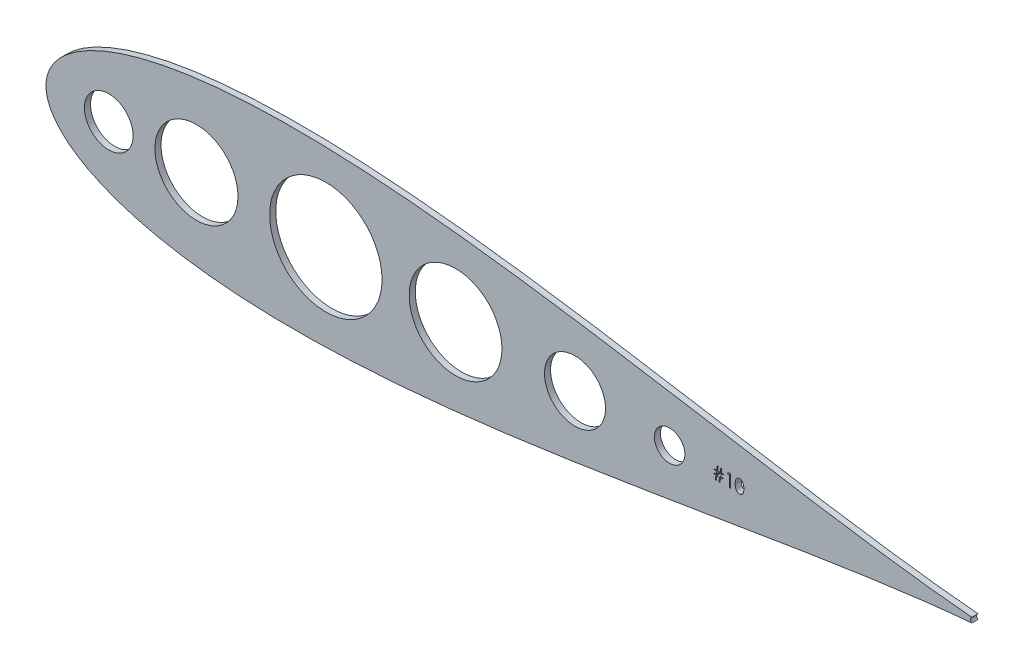
SolidWorks part; units mm, degrees
ref_plane "Front Plane" through (0, 0, 0) normal (0, 0, 1) x (1, 0, 0)
ref_plane "Top Plane" through (0, 0, 0) normal (0, 1, 0) x (1, 0, 0)
ref_plane "Right Plane" through (0, 0, 0) normal (1, 0, 0) x (0, 0, -1)
sketch "Model" plane through (0, 0, 0) normal (0, 0, 1) x (1, 0, 0)
  line L0 (632.1834, 567.3179) -> (632.1834, 572.0669)
  line L1 (632.6583, 567.3179) -> (632.1834, 567.3179)
  line L2 (632.6583, 572.6096) -> (632.6583, 567.3179)
  line L3 (631.6799, 572.6096) -> (632.6583, 572.6096)
  line L4 (631.3693, 572.0669) -> (631.6799, 572.6096)
  line L5 (632.1834, 572.0669) -> (631.3693, 572.0669)
  line L6 (629.6733, 570.71) -> (628.7595, 570.71)
  line L7 (629.6733, 571.0492) -> (629.6733, 570.71)
  line L8 (628.8104, 571.0492) -> (629.6733, 571.0492)
  line L9 (629.0648, 572.7453) -> (628.8104, 571.0492)
  line L10 (628.6556, 572.7453) -> (629.0648, 572.7453)
  line L11 (628.4012, 571.0492) -> (628.6556, 572.7453)
  line L12 (627.3179, 571.0492) -> (628.4012, 571.0492)
  line L13 (627.5723, 572.7453) -> (627.3179, 571.0492)
  line L14 (627.1631, 572.7453) -> (627.5723, 572.7453)
  line L15 (626.9087, 571.0492) -> (627.1631, 572.7453)
  line L16 (625.8741, 571.0492) -> (626.9087, 571.0492)
  line L17 (625.8741, 570.71) -> (625.8741, 571.0492)
  line L18 (626.8578, 570.71) -> (625.8741, 570.71)
  line L19 (626.6744, 569.4889) -> (626.8578, 570.71)
  line L20 (625.7384, 569.4889) -> (626.6744, 569.4889)
  line L21 (625.7384, 569.1497) -> (625.7384, 569.4889)
  line L22 (626.6236, 569.1497) -> (625.7384, 569.1497)
  line L23 (626.349, 567.3179) -> (626.6236, 569.1497)
  line L24 (626.7592, 567.3179) -> (626.349, 567.3179)
  line L25 (627.0338, 569.1497) -> (626.7592, 567.3179)
  line L26 (628.1161, 569.1497) -> (627.0338, 569.1497)
  line L27 (627.8415, 567.3179) -> (628.1161, 569.1497)
  line L28 (628.2518, 567.3179) -> (627.8415, 567.3179)
  line L29 (628.5263, 569.1497) -> (628.2518, 567.3179)
  line L30 (629.5376, 569.1497) -> (628.5263, 569.1497)
  line L31 (629.5376, 569.4889) -> (629.5376, 569.1497)
  line L32 (628.5772, 569.4889) -> (629.5376, 569.4889)
  line L33 (628.7595, 570.71) -> (628.5772, 569.4889)
  line L34 (627.267, 570.71) -> (627.0847, 569.4889)
  line L35 (628.3503, 570.71) -> (627.267, 570.71)
  line L36 (628.167, 569.4889) -> (628.3503, 570.71)
  line L37 (627.0847, 569.4889) -> (628.167, 569.4889)
  arc A0 (733.0945, 571.1452) -> (733.0926, 569.082) centre (733.7898, 570.113) ccw
  circle A1 centre (374.0091, 570.113) radius 10.1301
  circle A2 centre (607.3416, 570.113) radius 6.35
  circle A3 centre (567.9716, 570.113) radius 12.7
  circle A4 centre (518.2881, 570.113) radius 19.3008
  circle A5 centre (464.3241, 570.113) radius 23.3784
  circle A6 centre (410.4916, 570.1137) radius 17.272
  spline S0 degree 3 poles (733.0945, 571.1452) (731.0717, 571.3179) (726.7738, 571.7153) (719.931, 572.4271) (712.3349, 573.3017) (704.0224, 574.3433) (695.0324, 575.5531) (685.4036, 576.9284) (675.1779, 578.462) (664.3986, 580.143) (653.1109, 581.9565) (641.3614, 583.8836) (629.1982, 585.9022) (616.6704, 587.9868) (603.8283, 590.1092) (590.7233, 592.2384) (577.4078, 594.342) (563.9349, 596.3855) (550.3591, 598.3339) (536.7354, 600.1516) (523.1201, 601.8031) (509.5703, 603.2536) (496.1441, 604.4696) (482.9006, 605.4195) (469.9, 606.074) (457.2032, 606.4066) (444.8723, 606.3942) (432.9703, 606.0174) (421.5609, 605.2612) (410.7094, 604.1149) (400.482, 602.5731) (390.9469, 600.6353) (382.1748, 598.3081) (374.2396, 595.6051) (367.2206, 592.5504) (361.2031, 589.1843) (356.2769, 585.5753) (352.525, 581.8411) (349.9848, 578.1793) (348.5684, 574.8757) (347.9964, 572.2255) (347.8662, 570.1137) (347.9964, 568.0019) (348.5684, 565.3517) (349.9848, 562.0481) (352.525, 558.3863) (356.2769, 554.6521) (361.2031, 551.0431) (367.2206, 547.677) (374.2396, 544.6223) (382.1748, 541.9193) (390.9469, 539.5921) (400.482, 537.6543) (410.7094, 536.1125) (421.5609, 534.9662) (432.9703, 534.21) (444.8723, 533.8332) (457.2032, 533.8208) (469.9, 534.1534) (482.9006, 534.8078) (496.1441, 535.7578) (509.5703, 536.9738) (523.1201, 538.4243) (536.7354, 540.0758) (550.3591, 541.8935) (563.9349, 543.8419) (577.4078, 545.8854) (590.7233, 547.989) (603.8283, 550.1182) (616.6704, 552.2406) (629.1982, 554.3252) (641.3614, 556.3438) (653.1109, 558.2709) (664.3986, 560.0844) (675.1779, 561.7654) (685.4036, 563.299) (695.0324, 564.6743) (704.0224, 565.8841) (712.3349, 566.9257) (719.931, 567.8003) (726.7732, 568.5121) (731.0705, 568.9094) (733.0926, 569.082) knots 0.021301 0.021301 0.021301 0.021301 0.028553 0.036781 0.04592 0.055932 0.066773 0.078397 0.090755 0.103793 0.117456 0.131686 0.146422 0.1616 0.177156 0.193024 0.209135 0.225421 0.241812 0.258238 0.274629 0.290914 0.307025 0.322893 0.338448 0.353626 0.368361 0.38259 0.396253 0.40929 0.421647 0.43327 0.444109 0.454119 0.463255 0.471479 0.478755 0.485052 0.490344 0.49461 0.497833 0.5 0.502167 0.50539 0.509656 0.514948 0.521245 0.528521 0.536745 0.545881 0.555891 0.56673 0.578353 0.59071 0.603747 0.61741 0.631639 0.646374 0.661552 0.677107 0.692975 0.709086 0.725371 0.741762 0.758188 0.774579 0.790865 0.806976 0.822844 0.8384 0.853578 0.868314 0.882544 0.896207 0.909245 0.921603 0.933227 0.944068 0.95408 0.963219 0.971447 0.978697 0.978697 0.978697 0.978697
  spline S1 degree 3 poles (638.2213, 569.9616) (638.2203, 569.8807) (638.2184, 569.723) (638.2085, 569.4924) (638.1889, 569.2747) (638.1644, 569.0694) (638.1304, 568.8773) (638.0887, 568.6978) (638.0424, 568.53) (637.9852, 568.3754) (637.9226, 568.2319) (637.8544, 568.0978) (637.7815, 567.9721) (637.7019, 567.8557) (637.6172, 567.7478) (637.5254, 567.6502) (637.4291, 567.5608) (637.3272, 567.4812) (637.2208, 567.4115) (637.112, 567.3492) (636.9989, 567.2989) (636.8841, 567.2558) (636.766, 567.2228) (636.6447, 567.2001) (636.5208, 567.1841) (636.437, 567.1829) (636.3949, 567.1822) knots 0 0 0 0 0.065063 0.126773 0.185516 0.240765 0.29298 0.34225 0.388919 0.432776 0.474628 0.514775 0.553606 0.591426 0.628028 0.663804 0.698984 0.733591 0.767628 0.801208 0.834264 0.866981 0.89972 0.932702 0.966176 1 1 1 1
  spline S2 degree 3 poles (636.3949, 572.7453) (636.437, 572.7445) (636.5207, 572.7431) (636.6444, 572.729) (636.7653, 572.7056) (636.8828, 572.6724) (636.9979, 572.6313) (637.1097, 572.5798) (637.2188, 572.5198) (637.3237, 572.4493) (637.4253, 572.3707) (637.5212, 572.2819) (637.6115, 572.1837) (637.6971, 572.0772) (637.7758, 571.9603) (637.8508, 571.8352) (637.9179, 571.6995) (637.9825, 571.5556) (638.0383, 571.3995) (638.0886, 571.232) (638.1292, 571.0512) (638.163, 570.8581) (638.1893, 570.6518) (638.2084, 570.433) (638.2185, 570.2013) (638.2204, 570.0429) (638.2213, 569.9616) knots 0 0 0 0 0.033788 0.067194 0.099862 0.132567 0.165151 0.197913 0.231319 0.265083 0.299255 0.334399 0.369943 0.406284 0.444064 0.482998 0.523354 0.565537 0.609613 0.656391 0.705885 0.758325 0.813832 0.872795 0.934722 1 1 1 1
  spline S3 degree 3 poles (634.6257, 569.9616) (634.6262, 570.0465) (634.6272, 570.2112) (634.6379, 570.4513) (634.6557, 570.6765) (634.6801, 570.8869) (634.7098, 571.0824) (634.7494, 571.2627) (634.7945, 571.4285) (634.8467, 571.5804) (634.9057, 571.7203) (634.9698, 571.851) (635.0417, 571.9722) (635.1173, 572.0858) (635.1996, 572.1899) (635.2862, 572.2862) (635.3806, 572.3722) (635.4795, 572.4506) (635.5838, 572.5193) (635.6906, 572.5798) (635.8006, 572.6315) (635.9141, 572.6722) (636.0301, 572.7058) (636.149, 572.7287) (636.2709, 572.7432) (636.3532, 572.7446) (636.3949, 572.7453) knots 0 0 0 0 0.068595 0.133246 0.194313 0.251279 0.304513 0.354235 0.400481 0.443411 0.484015 0.523252 0.561042 0.5979 0.633518 0.668314 0.702496 0.736685 0.770293 0.803437 0.835913 0.86846 0.900847 0.933467 0.966258 1 1 1 1
  spline S4 degree 3 poles (636.3949, 567.1822) (636.3532, 567.1829) (636.2709, 567.1843) (636.1489, 567.1987) (636.0306, 567.2218) (635.9152, 567.2542) (635.8023, 567.2939) (635.6933, 567.3455) (635.587, 567.405) (635.4838, 567.4727) (635.3855, 567.5503) (635.2916, 567.6361) (635.2045, 567.7323) (635.1234, 567.8373) (635.0463, 567.9503) (634.9754, 568.0726) (634.9098, 568.2039) (634.8499, 568.345) (634.7968, 568.498) (634.7498, 568.6645) (634.7127, 568.8461) (634.681, 569.0413) (634.6554, 569.251) (634.638, 569.4752) (634.6272, 569.7138) (634.6262, 569.8775) (634.6257, 569.9616) knots 0 0 0 0 0.033787 0.066622 0.099285 0.131361 0.163585 0.196104 0.228902 0.262158 0.295991 0.330218 0.36506 0.400951 0.43762 0.475708 0.515381 0.556414 0.599765 0.646424 0.696431 0.749782 0.806573 0.867436 0.931887 1 1 1 1
  spline S5 degree 3 poles (637.5461, 568.6334) (637.562, 568.6806) (637.5944, 568.7765) (637.6362, 568.9252) (637.6691, 569.0813) (637.6986, 569.2437) (637.7188, 569.4137) (637.7351, 569.5907) (637.7447, 569.775) (637.7458, 569.9001) (637.7464, 569.9638) knots 0 0 0 0 0.110588 0.224542 0.342503 0.464324 0.590756 0.722227 0.858843 1 1 1 1
  spline S6 degree 3 poles (636.4108, 572.2025) (636.3523, 572.1995) (636.2351, 572.1933) (636.0621, 572.1499) (635.8962, 572.0743) (635.7643, 571.9912) (635.6632, 571.9121) (635.592, 571.8435) (635.5253, 571.7684) (635.4638, 571.6862) (635.4062, 571.5978) (635.3533, 571.5026) (635.3057, 571.4) (635.2617, 571.2902) (635.223, 571.1699) (635.1912, 571.0372) (635.1617, 570.8914) (635.1408, 570.7315) (635.1223, 570.5587) (635.1104, 570.3723) (635.1011, 570.1727) (635.1008, 570.0348) (635.1006, 569.9638) knots 0 0 0 0 0.060387 0.120883 0.182755 0.247811 0.281299 0.315088 0.349702 0.384857 0.420966 0.458511 0.497175 0.537602 0.580503 0.627468 0.678388 0.733983 0.793747 0.857714 0.926698 1 1 1 1
  spline S7 degree 3 poles (636.4108, 567.725) (636.4694, 567.7274) (636.5865, 567.7322) (636.7575, 567.7788) (636.9236, 567.849) (637.0537, 567.9321) (637.1527, 568.0112) (637.2236, 568.0787) (637.2888, 568.1542) (637.3505, 568.2357) (637.4071, 568.3247) (637.4586, 568.4208) (637.5056, 568.5243) (637.5324, 568.5965) (637.5461, 568.6334) knots 0 0 0 0 0.112813 0.225394 0.339595 0.459675 0.521735 0.583926 0.648174 0.713881 0.781004 0.851451 0.924051 1 1 1 1
  spline S8 degree 3 poles (635.1006, 569.9638) (635.1008, 569.8931) (635.1011, 569.7559) (635.1103, 569.5566) (635.1228, 569.3706) (635.1389, 569.1979) (635.1628, 569.0389) (635.1895, 568.8926) (635.2221, 568.7598) (635.2606, 568.6394) (635.3046, 568.5296) (635.3525, 568.4274) (635.404, 568.3316) (635.4616, 568.2431) (635.5244, 568.1616) (635.5909, 568.0857) (635.6635, 568.0179) (635.7641, 567.9367) (635.8968, 567.8528) (636.0641, 567.7797) (636.2359, 567.7337) (636.3526, 567.7279) (636.4108, 567.725) knots 0 0 0 0 0.072951 0.141584 0.205926 0.265301 0.320597 0.371817 0.41879 0.461699 0.502134 0.540804 0.578181 0.614297 0.649678 0.684299 0.718359 0.752081 0.817652 0.879722 0.939966 1 1 1 1
  spline S9 degree 3 poles (637.7464, 569.9638) (637.7456, 570.0274) (637.744, 570.1518) (637.7378, 570.334) (637.7217, 570.5071) (637.7039, 570.6717) (637.6776, 570.8271) (637.6492, 570.9744) (637.6111, 571.1119) (637.5704, 571.2417) (637.5238, 571.3624) (637.4725, 571.4744) (637.4178, 571.5784) (637.3583, 571.6741) (637.2948, 571.7618) (637.2256, 571.8399) (637.1535, 571.9107) (637.0525, 571.9915) (636.9202, 572.0739) (636.7557, 572.1498) (636.5844, 572.1933) (636.4686, 572.1995) (636.4108, 572.2025) knots 0 0 0 0 0.065681 0.128486 0.188175 0.245106 0.299448 0.350823 0.399942 0.446672 0.491255 0.533376 0.573853 0.612526 0.649597 0.685532 0.720106 0.753838 0.818925 0.880493 0.940311 1 1 1 1
sketch "Sketch2" plane through (0, 0, 0) normal (0, 0, 1) x (1, 0, 0)
  line L0 (632.1834, 567.3179) -> (632.1834, 572.0669)
  line L1 (632.6583, 567.3179) -> (632.1834, 567.3179)
  line L2 (632.6583, 572.6096) -> (632.6583, 567.3179)
  line L3 (631.6799, 572.6096) -> (632.6583, 572.6096)
  line L4 (631.3693, 572.0669) -> (631.6799, 572.6096)
  line L5 (632.1834, 572.0669) -> (631.3693, 572.0669)
  line L6 (629.6733, 570.71) -> (628.7595, 570.71)
  line L7 (629.6733, 571.0492) -> (629.6733, 570.71)
  line L8 (628.8104, 571.0492) -> (629.6733, 571.0492)
  line L9 (629.0648, 572.7453) -> (628.8104, 571.0492)
  line L10 (628.6556, 572.7453) -> (629.0648, 572.7453)
  line L11 (628.4012, 571.0492) -> (628.6556, 572.7453)
  line L12 (627.3179, 571.0492) -> (628.4012, 571.0492)
  line L13 (627.5723, 572.7453) -> (627.3179, 571.0492)
  line L14 (627.1631, 572.7453) -> (627.5723, 572.7453)
  line L15 (626.9087, 571.0492) -> (627.1631, 572.7453)
  line L16 (625.8741, 571.0492) -> (626.9087, 571.0492)
  line L17 (625.8741, 570.71) -> (625.8741, 571.0492)
  line L18 (626.8578, 570.71) -> (625.8741, 570.71)
  line L19 (626.6744, 569.4889) -> (626.8578, 570.71)
  line L20 (625.7384, 569.4889) -> (626.6744, 569.4889)
  line L21 (625.7384, 569.1497) -> (625.7384, 569.4889)
  line L22 (626.6236, 569.1497) -> (625.7384, 569.1497)
  line L23 (626.349, 567.3179) -> (626.6236, 569.1497)
  line L24 (626.7592, 567.3179) -> (626.349, 567.3179)
  line L25 (627.0338, 569.1497) -> (626.7592, 567.3179)
  line L26 (628.1161, 569.1497) -> (627.0338, 569.1497)
  line L27 (627.8415, 567.3179) -> (628.1161, 569.1497)
  line L28 (628.2518, 567.3179) -> (627.8415, 567.3179)
  line L29 (628.5263, 569.1497) -> (628.2518, 567.3179)
  line L30 (629.5376, 569.1497) -> (628.5263, 569.1497)
  line L31 (629.5376, 569.4889) -> (629.5376, 569.1497)
  line L32 (628.5772, 569.4889) -> (629.5376, 569.4889)
  line L33 (628.7595, 570.71) -> (628.5772, 569.4889)
  line L34 (627.267, 570.71) -> (627.0847, 569.4889)
  line L35 (628.3503, 570.71) -> (627.267, 570.71)
  line L36 (628.167, 569.4889) -> (628.3503, 570.71)
  line L37 (627.0847, 569.4889) -> (628.167, 569.4889)
  arc A0 (733.0945, 571.1452) -> (733.0926, 569.082) centre (733.7898, 570.113) ccw
  circle A1 centre (374.0091, 570.113) radius 10.1301
  circle A2 centre (607.3416, 570.113) radius 6.35
  circle A3 centre (567.9716, 570.113) radius 12.7
  circle A4 centre (518.2881, 570.113) radius 19.3008
  circle A5 centre (464.3241, 570.113) radius 23.3784
  circle A6 centre (410.4916, 570.1137) radius 17.272
  spline S0 degree 3 poles (733.0945, 571.1452) (731.0717, 571.3179) (726.7738, 571.7153) (719.931, 572.4271) (712.3349, 573.3017) (704.0224, 574.3433) (695.0324, 575.5531) (685.4036, 576.9284) (675.1779, 578.462) (664.3986, 580.143) (653.1109, 581.9565) (641.3614, 583.8836) (629.1982, 585.9022) (616.6704, 587.9868) (603.8283, 590.1092) (590.7233, 592.2384) (577.4078, 594.342) (563.9349, 596.3855) (550.3591, 598.3339) (536.7354, 600.1516) (523.1201, 601.8031) (509.5703, 603.2536) (496.1441, 604.4696) (482.9006, 605.4195) (469.9, 606.074) (457.2032, 606.4066) (444.8723, 606.3942) (432.9703, 606.0174) (421.5609, 605.2612) (410.7094, 604.1149) (400.482, 602.5731) (390.9469, 600.6353) (382.1748, 598.3081) (374.2396, 595.6051) (367.2206, 592.5504) (361.2031, 589.1843) (356.2769, 585.5753) (352.525, 581.8411) (349.9848, 578.1793) (348.5684, 574.8757) (347.9964, 572.2255) (347.8662, 570.1137) (347.9964, 568.0019) (348.5684, 565.3517) (349.9848, 562.0481) (352.525, 558.3863) (356.2769, 554.6521) (361.2031, 551.0431) (367.2206, 547.677) (374.2396, 544.6223) (382.1748, 541.9193) (390.9469, 539.5921) (400.482, 537.6543) (410.7094, 536.1125) (421.5609, 534.9662) (432.9703, 534.21) (444.8723, 533.8332) (457.2032, 533.8208) (469.9, 534.1534) (482.9006, 534.8078) (496.1441, 535.7578) (509.5703, 536.9738) (523.1201, 538.4243) (536.7354, 540.0758) (550.3591, 541.8935) (563.9349, 543.8419) (577.4078, 545.8854) (590.7233, 547.989) (603.8283, 550.1182) (616.6704, 552.2406) (629.1982, 554.3252) (641.3614, 556.3438) (653.1109, 558.2709) (664.3986, 560.0844) (675.1779, 561.7654) (685.4036, 563.299) (695.0324, 564.6743) (704.0224, 565.8841) (712.3349, 566.9257) (719.931, 567.8003) (726.7732, 568.5121) (731.0705, 568.9094) (733.0926, 569.082) knots 0.021301 0.021301 0.021301 0.021301 0.028553 0.036781 0.04592 0.055932 0.066773 0.078397 0.090755 0.103793 0.117456 0.131686 0.146422 0.1616 0.177156 0.193024 0.209135 0.225421 0.241812 0.258238 0.274629 0.290914 0.307025 0.322893 0.338448 0.353626 0.368361 0.38259 0.396253 0.40929 0.421647 0.43327 0.444109 0.454119 0.463255 0.471479 0.478755 0.485052 0.490344 0.49461 0.497833 0.5 0.502167 0.50539 0.509656 0.514948 0.521245 0.528521 0.536745 0.545881 0.555891 0.56673 0.578353 0.59071 0.603747 0.61741 0.631639 0.646374 0.661552 0.677107 0.692975 0.709086 0.725371 0.741762 0.758188 0.774579 0.790865 0.806976 0.822844 0.8384 0.853578 0.868314 0.882544 0.896207 0.909245 0.921603 0.933227 0.944068 0.95408 0.963219 0.971447 0.978697 0.978697 0.978697 0.978697
  spline S1 degree 3 poles (638.2213, 569.9616) (638.2203, 569.8807) (638.2184, 569.723) (638.2085, 569.4924) (638.1889, 569.2747) (638.1644, 569.0694) (638.1304, 568.8773) (638.0887, 568.6978) (638.0424, 568.53) (637.9852, 568.3754) (637.9226, 568.2319) (637.8544, 568.0978) (637.7815, 567.9721) (637.7019, 567.8557) (637.6172, 567.7478) (637.5254, 567.6502) (637.4291, 567.5608) (637.3272, 567.4812) (637.2208, 567.4115) (637.112, 567.3492) (636.9989, 567.2989) (636.8841, 567.2558) (636.766, 567.2228) (636.6447, 567.2001) (636.5208, 567.1841) (636.437, 567.1829) (636.3949, 567.1822) knots 0 0 0 0 0.065063 0.126773 0.185516 0.240765 0.29298 0.34225 0.388919 0.432776 0.474628 0.514775 0.553606 0.591426 0.628028 0.663804 0.698984 0.733591 0.767628 0.801208 0.834264 0.866981 0.89972 0.932702 0.966176 1 1 1 1
  spline S2 degree 3 poles (636.3949, 572.7453) (636.437, 572.7445) (636.5207, 572.7431) (636.6444, 572.729) (636.7653, 572.7056) (636.8828, 572.6724) (636.9979, 572.6313) (637.1097, 572.5798) (637.2188, 572.5198) (637.3237, 572.4493) (637.4253, 572.3707) (637.5212, 572.2819) (637.6115, 572.1837) (637.6971, 572.0772) (637.7758, 571.9603) (637.8508, 571.8352) (637.9179, 571.6995) (637.9825, 571.5556) (638.0383, 571.3995) (638.0886, 571.232) (638.1292, 571.0512) (638.163, 570.8581) (638.1893, 570.6518) (638.2084, 570.433) (638.2185, 570.2013) (638.2204, 570.0429) (638.2213, 569.9616) knots 0 0 0 0 0.033788 0.067194 0.099862 0.132567 0.165151 0.197913 0.231319 0.265083 0.299255 0.334399 0.369943 0.406284 0.444064 0.482998 0.523354 0.565537 0.609613 0.656391 0.705885 0.758325 0.813832 0.872795 0.934722 1 1 1 1
  spline S3 degree 3 poles (634.6257, 569.9616) (634.6262, 570.0465) (634.6272, 570.2112) (634.6379, 570.4513) (634.6557, 570.6765) (634.6801, 570.8869) (634.7098, 571.0824) (634.7494, 571.2627) (634.7945, 571.4285) (634.8467, 571.5804) (634.9057, 571.7203) (634.9698, 571.851) (635.0417, 571.9722) (635.1173, 572.0858) (635.1996, 572.1899) (635.2862, 572.2862) (635.3806, 572.3722) (635.4795, 572.4506) (635.5838, 572.5193) (635.6906, 572.5798) (635.8006, 572.6315) (635.9141, 572.6722) (636.0301, 572.7058) (636.149, 572.7287) (636.2709, 572.7432) (636.3532, 572.7446) (636.3949, 572.7453) knots 0 0 0 0 0.068595 0.133246 0.194313 0.251279 0.304513 0.354235 0.400481 0.443411 0.484015 0.523252 0.561042 0.5979 0.633518 0.668314 0.702496 0.736685 0.770293 0.803437 0.835913 0.86846 0.900847 0.933467 0.966258 1 1 1 1
  spline S4 degree 3 poles (636.3949, 567.1822) (636.3532, 567.1829) (636.2709, 567.1843) (636.1489, 567.1987) (636.0306, 567.2218) (635.9152, 567.2542) (635.8023, 567.2939) (635.6933, 567.3455) (635.587, 567.405) (635.4838, 567.4727) (635.3855, 567.5503) (635.2916, 567.6361) (635.2045, 567.7323) (635.1234, 567.8373) (635.0463, 567.9503) (634.9754, 568.0726) (634.9098, 568.2039) (634.8499, 568.345) (634.7968, 568.498) (634.7498, 568.6645) (634.7127, 568.8461) (634.681, 569.0413) (634.6554, 569.251) (634.638, 569.4752) (634.6272, 569.7138) (634.6262, 569.8775) (634.6257, 569.9616) knots 0 0 0 0 0.033787 0.066622 0.099285 0.131361 0.163585 0.196104 0.228902 0.262158 0.295991 0.330218 0.36506 0.400951 0.43762 0.475708 0.515381 0.556414 0.599765 0.646424 0.696431 0.749782 0.806573 0.867436 0.931887 1 1 1 1
  spline S5 degree 3 poles (637.5461, 568.6334) (637.562, 568.6806) (637.5944, 568.7765) (637.6362, 568.9252) (637.6691, 569.0813) (637.6986, 569.2437) (637.7188, 569.4137) (637.7351, 569.5907) (637.7447, 569.775) (637.7458, 569.9001) (637.7464, 569.9638) knots 0 0 0 0 0.110588 0.224542 0.342503 0.464324 0.590756 0.722227 0.858843 1 1 1 1
  spline S6 degree 3 poles (636.4108, 572.2025) (636.3523, 572.1995) (636.2351, 572.1933) (636.0621, 572.1499) (635.8962, 572.0743) (635.7643, 571.9912) (635.6632, 571.9121) (635.592, 571.8435) (635.5253, 571.7684) (635.4638, 571.6862) (635.4062, 571.5978) (635.3533, 571.5026) (635.3057, 571.4) (635.2617, 571.2902) (635.223, 571.1699) (635.1912, 571.0372) (635.1617, 570.8914) (635.1408, 570.7315) (635.1223, 570.5587) (635.1104, 570.3723) (635.1011, 570.1727) (635.1008, 570.0348) (635.1006, 569.9638) knots 0 0 0 0 0.060387 0.120883 0.182755 0.247811 0.281299 0.315088 0.349702 0.384857 0.420966 0.458511 0.497175 0.537602 0.580503 0.627468 0.678388 0.733983 0.793747 0.857714 0.926698 1 1 1 1
  spline S7 degree 3 poles (636.4108, 567.725) (636.4694, 567.7274) (636.5865, 567.7322) (636.7575, 567.7788) (636.9236, 567.849) (637.0537, 567.9321) (637.1527, 568.0112) (637.2236, 568.0787) (637.2888, 568.1542) (637.3505, 568.2357) (637.4071, 568.3247) (637.4586, 568.4208) (637.5056, 568.5243) (637.5324, 568.5965) (637.5461, 568.6334) knots 0 0 0 0 0.112813 0.225394 0.339595 0.459675 0.521735 0.583926 0.648174 0.713881 0.781004 0.851451 0.924051 1 1 1 1
  spline S8 degree 3 poles (635.1006, 569.9638) (635.1008, 569.8931) (635.1011, 569.7559) (635.1103, 569.5566) (635.1228, 569.3706) (635.1389, 569.1979) (635.1628, 569.0389) (635.1895, 568.8926) (635.2221, 568.7598) (635.2606, 568.6394) (635.3046, 568.5296) (635.3525, 568.4274) (635.404, 568.3316) (635.4616, 568.2431) (635.5244, 568.1616) (635.5909, 568.0857) (635.6635, 568.0179) (635.7641, 567.9367) (635.8968, 567.8528) (636.0641, 567.7797) (636.2359, 567.7337) (636.3526, 567.7279) (636.4108, 567.725) knots 0 0 0 0 0.072951 0.141584 0.205926 0.265301 0.320597 0.371817 0.41879 0.461699 0.502134 0.540804 0.578181 0.614297 0.649678 0.684299 0.718359 0.752081 0.817652 0.879722 0.939966 1 1 1 1
  spline S9 degree 3 poles (637.7464, 569.9638) (637.7456, 570.0274) (637.744, 570.1518) (637.7378, 570.334) (637.7217, 570.5071) (637.7039, 570.6717) (637.6776, 570.8271) (637.6492, 570.9744) (637.6111, 571.1119) (637.5704, 571.2417) (637.5238, 571.3624) (637.4725, 571.4744) (637.4178, 571.5784) (637.3583, 571.6741) (637.2948, 571.7618) (637.2256, 571.8399) (637.1535, 571.9107) (637.0525, 571.9915) (636.9202, 572.0739) (636.7557, 572.1498) (636.5844, 572.1933) (636.4686, 572.1995) (636.4108, 572.2025) knots 0 0 0 0 0.065681 0.128486 0.188175 0.245106 0.299448 0.350823 0.399942 0.446672 0.491255 0.533376 0.573853 0.612526 0.649597 0.685532 0.720106 0.753838 0.818925 0.880493 0.940311 1 1 1 1
extrude "Boss-Extrude1" add sketch "Sketch2" along normal blind 2.54 contours A0 S0 L6 L33 L32 L31 L30 L29 L28 L27 L26 L25 L24 L23 L22 L21 L20 L19 L18 L17 L16 L15 L14 L13 L12 L11 L10 L9 L8 L7 L0 L5 L4 L3 L2 L1 A1 A2 A3 A4 A5 A6
